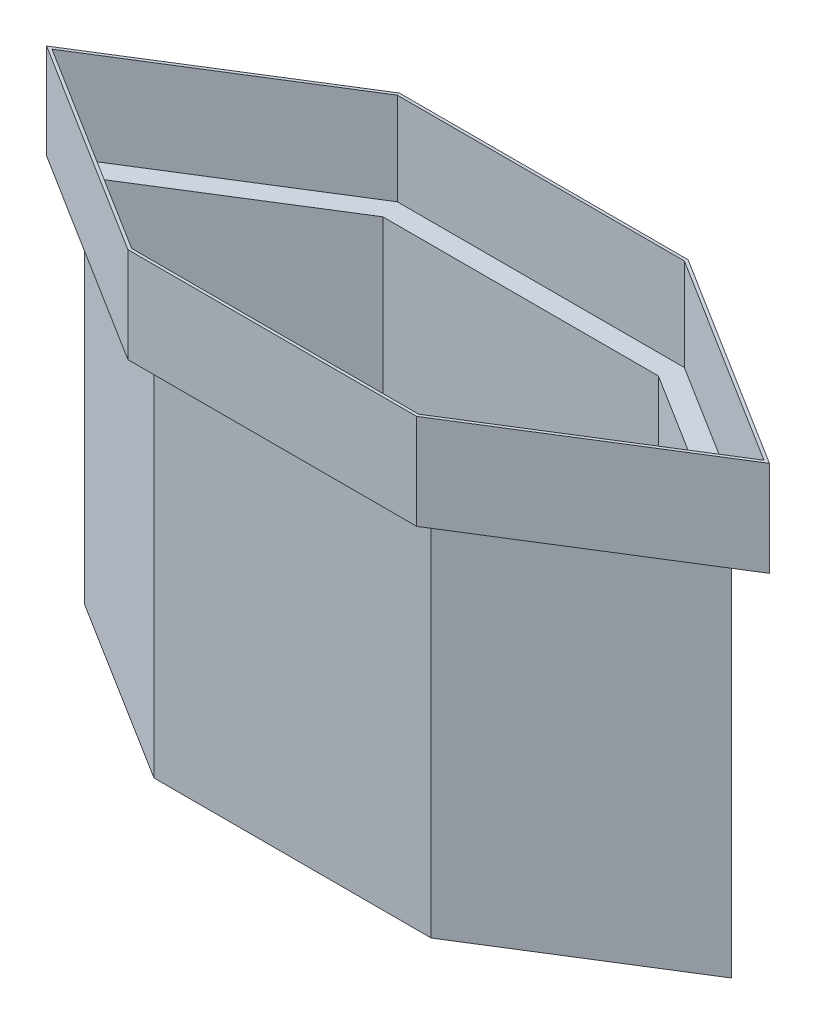
SolidWorks part; units mm, degrees
ref_plane "Front Plane" through (0, 0, 0) normal (0, 0, 1) x (1, 0, 0)
ref_plane "Top Plane" through (0, 0, 0) normal (0, 1, 0) x (1, 0, 0)
ref_plane "Right Plane" through (0, 0, 0) normal (1, 0, 0) x (0, 0, -1)
sketch "Sketch2" plane through (0, 0, 0) normal (0, 1, 0) x (1, 0, 0)
  line L0 (-152.4, 127) -> (-355.6, 0)
  line L1 (152.4, -127) -> (-152.4, -127)
  line L2 (-355.6, 0) -> (355.6, 0) construction
  line L3 (152.4, 127) -> (-152.4, 127)
  line L4 (-152.4, 127) -> (-152.4, -127) construction
  line L5 (152.4, -127) -> (-152.4, 127) construction
  line L6 (152.4, 127) -> (-152.4, -127) construction
  line L7 (-355.6, 0) -> (-152.4, -127)
  line L8 (152.4, 127) -> (355.6, 0)
  line L9 (355.6, 0) -> (152.4, -127)
  line L10 (152.4, 127) -> (152.4, -127) construction
  point P0 (0, 0)
  point P8 (0, 0)
  dimension "D1" = 304.8
  dimension "D2" = 203.2
  dimension "D3" = 254
extrude "Boss-Extrude1" add sketch "Sketch2" along normal blind 3.175
sketch "Sketch3" plane through (0, 3.175, 0) normal (0, 1, 0) x (1, 0, 0)
  line L0 (152.4, -127) -> (355.6, 0) construction
  line L1 (355.6, 0) -> (152.4, 127) construction
  line L2 (152.4, 127) -> (-152.4, 127) construction
  line L3 (-152.4, 127) -> (-355.6, 0) construction
  line L4 (-355.6, 0) -> (-152.4, -127) construction
  line L5 (-152.4, -127) -> (152.4, -127) construction
  line L6 (152.4, -127) -> (355.6, 0)
  line L7 (355.6, 0) -> (152.4, 127)
  line L8 (152.4, 127) -> (-152.4, 127)
  line L9 (-152.4, 127) -> (-355.6, 0)
  line L10 (-355.6, 0) -> (-152.4, -127)
  line L11 (-152.4, -127) -> (152.4, -127)
  line L12 (151.4894, -123.825) -> (349.6094, 0)
  line L13 (349.6094, 0) -> (151.4894, 123.825)
  line L14 (151.4894, 123.825) -> (-151.4894, 123.825)
  line L15 (-151.4894, 123.825) -> (-349.6094, 0)
  line L16 (-349.6094, 0) -> (-151.4894, -123.825)
  line L17 (-151.4894, -123.825) -> (151.4894, -123.825)
  dimension "D1" = 3.175
extrude "Boss-Extrude2" add sketch "Sketch3" along normal blind 403.225
sketch "Sketch5" plane through (0, 406.4, 0) normal (0, 1, 0) x (1, 0, 0)
  line L0 (151.4894, 123.825) -> (-151.4894, 123.825) construction
  line L1 (-151.4894, 123.825) -> (-349.6094, 0) construction
  line L2 (-349.6094, 0) -> (-151.4894, -123.825) construction
  line L3 (-151.4894, -123.825) -> (151.4894, -123.825) construction
  line L4 (151.4894, -123.825) -> (349.6094, 0) construction
  line L5 (349.6094, 0) -> (151.4894, 123.825) construction
  line L6 (151.4894, 123.825) -> (-151.4894, 123.825)
  line L7 (-151.4894, 123.825) -> (-349.6094, 0)
  line L8 (-349.6094, 0) -> (-151.4894, -123.825)
  line L9 (-151.4894, -123.825) -> (151.4894, -123.825)
  line L10 (151.4894, -123.825) -> (349.6094, 0)
  line L11 (349.6094, 0) -> (151.4894, 123.825)
  line L12 (158.774, 149.225) -> (-158.774, 149.225)
  line L13 (-158.774, 149.225) -> (-397.534, 0)
  line L14 (-397.534, 0) -> (-158.774, -149.225)
  line L15 (-158.774, -149.225) -> (158.774, -149.225)
  line L16 (158.774, -149.225) -> (397.534, 0)
  line L17 (397.534, 0) -> (158.774, 149.225)
  dimension "D1" = 25.4
extrude "Boss-Extrude3" add sketch "Sketch5" along normal blind 3.175
sketch "Sketch6" plane through (0, 409.575, 0) normal (0, 1, 0) x (1, 0, 0)
  line L0 (-158.774, 149.225) -> (-397.534, 0) construction
  line L1 (158.774, 149.225) -> (-158.774, 149.225) construction
  line L2 (-397.534, 0) -> (-158.774, -149.225) construction
  line L3 (397.534, 0) -> (158.774, 149.225) construction
  line L4 (158.774, -149.225) -> (397.534, 0) construction
  line L5 (-158.774, -149.225) -> (158.774, -149.225) construction
  line L6 (-158.774, 149.225) -> (-397.534, 0)
  line L7 (158.774, 149.225) -> (-158.774, 149.225)
  line L8 (-397.534, 0) -> (-158.774, -149.225)
  line L9 (397.534, 0) -> (158.774, 149.225)
  line L10 (158.774, -149.225) -> (397.534, 0)
  line L11 (-158.774, -149.225) -> (158.774, -149.225)
  line L12 (-157.8635, 146.05) -> (-391.5435, 0)
  line L13 (-391.5435, 0) -> (-157.8635, -146.05)
  line L14 (-157.8635, -146.05) -> (157.8635, -146.05)
  line L15 (157.8635, -146.05) -> (391.5435, 0)
  line L16 (391.5435, 0) -> (157.8635, 146.05)
  line L17 (157.8635, 146.05) -> (-157.8635, 146.05)
  dimension "D1" = 3.175
extrude "Boss-Extrude4" add sketch "Sketch6" along normal blind 101.6
sketch "Sketch7" plane through (0, 511.175, 0) normal (0, 1, 0) x (1, 0, 0)
  line L0 (-158.774, 149.225) -> (-397.534, 0) construction
  line L1 (-157.8635, 146.05) -> (-391.5435, 0) construction
  line L2 (-391.5435, 0) -> (-157.8635, -146.05) construction
  line L3 (-397.534, 0) -> (-158.774, -149.225) construction
  line L4 (158.774, 149.225) -> (-158.774, 149.225) construction
  line L5 (157.8635, 146.05) -> (-157.8635, 146.05) construction
  line L6 (397.534, 0) -> (158.774, 149.225) construction
  line L7 (391.5435, 0) -> (157.8635, 146.05) construction
  line L8 (157.8635, -146.05) -> (391.5435, 0) construction
  line L9 (158.774, -149.225) -> (397.534, 0) construction
  line L10 (-158.774, -149.225) -> (158.774, -149.225) construction
  line L11 (-157.8635, -146.05) -> (157.8635, -146.05) construction
  line L12 (-158.774, 149.225) -> (-397.534, 0)
  line L13 (-157.8635, 146.05) -> (-391.5435, 0)
  line L14 (-391.5435, 0) -> (-157.8635, -146.05)
  line L15 (-397.534, 0) -> (-158.774, -149.225)
  line L16 (158.774, 149.225) -> (-158.774, 149.225)
  line L17 (157.8635, 146.05) -> (-157.8635, 146.05)
  line L18 (397.534, 0) -> (158.774, 149.225)
  line L19 (391.5435, 0) -> (157.8635, 146.05)
  line L20 (157.8635, -146.05) -> (391.5435, 0)
  line L21 (158.774, -149.225) -> (397.534, 0)
  line L22 (-158.774, -149.225) -> (158.774, -149.225)
  line L23 (-157.8635, -146.05) -> (157.8635, -146.05)
ref_plane "Plane2" through (0, 714.375, 0) normal (0, 1, 0) x (1, 0, 0)
sketch "Sketch8" plane through (0, 714.375, 0) normal (0, 1, 0) x (1, 0, 0)
  line L0 (-158.774, 149.225) -> (-397.534, 0) construction
  line L1 (158.774, 149.225) -> (-158.774, 149.225) construction
  line L2 (397.534, 0) -> (158.774, 149.225) construction
  line L3 (158.774, -149.225) -> (397.534, 0) construction
  line L4 (-158.774, -149.225) -> (158.774, -149.225) construction
  line L5 (-397.534, 0) -> (-158.774, -149.225) construction
  line L6 (-158.774, 149.225) -> (-397.534, 0) construction
  line L7 (158.774, 149.225) -> (-158.774, 149.225) construction
  line L8 (397.534, 0) -> (158.774, 149.225) construction
  line L9 (158.774, -149.225) -> (397.534, 0) construction
  line L10 (-158.774, -149.225) -> (158.774, -149.225) construction
  line L11 (-397.534, 0) -> (-158.774, -149.225) construction
  line L12 (-189.6608, 256.9208) -> (-600.734, 0)
  line L13 (-600.734, 0) -> (-189.6608, -256.9208)
  line L14 (-189.6608, -256.9208) -> (189.6608, -256.9208)
  line L15 (189.6608, -256.9208) -> (600.734, 0)
  line L16 (600.734, 0) -> (189.6608, 256.9208)
  line L17 (189.6608, 256.9208) -> (-189.6608, 256.9208)
  line L18 (-188.7502, 253.7458) -> (-594.7435, 0)
  line L19 (-594.7435, 0) -> (-188.7502, -253.7458)
  line L20 (-188.7502, -253.7458) -> (188.7502, -253.7458)
  line L21 (188.7502, -253.7458) -> (594.7435, 0)
  line L22 (594.7435, 0) -> (188.7502, 253.7458)
  line L23 (188.7502, 253.7458) -> (-188.7502, 253.7458)
  dimension "D1" = 203.2
  dimension "D2" = 3.175
sketch3d "3DSketch1"
  line L0 (-600.734, 714.375, 0) -> (-397.534, 511.175, 0) construction
equation "\"D1@Boss-Extrude2\"=16.00000in-0.125"
